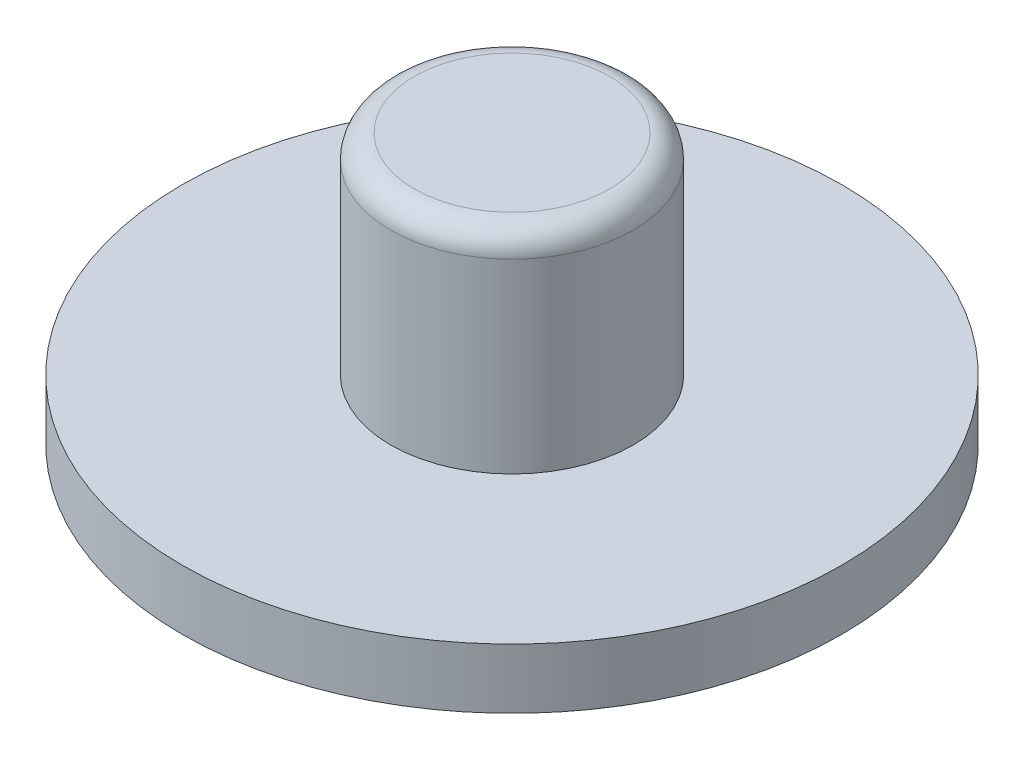
SolidWorks part; units mm, degrees
ref_plane "Front Plane" through (0, 0, 0) normal (0, 0, 1) x (1, 0, 0)
ref_plane "Top Plane" through (0, 0, 0) normal (0, 1, 0) x (1, 0, 0)
ref_plane "Right Plane" through (0, 0, 0) normal (1, 0, 0) x (0, 0, -1)
sketch "Sketch1" plane through (0, 0, 0) normal (0, 1, 0) x (1, 0, 0)
  circle A0 centre (0, 0) radius 4.05
  dimension "D1" = 8.1
extrude "Boss-Extrude1" add sketch "Sketch1" along normal mid plane 7
fillet "Fillet1" radius 0.7937 1 edges at (0, 3.5, 4.05)
sketch "Sketch2" plane through (0, -3.5, 0) normal (0, -1, 0) x (1, 0, 0)
  circle A0 centre (0, 0) radius 11
  dimension "D1" = 22
extrude "Boss-Extrude2" add sketch "Sketch2" along normal blind 2
